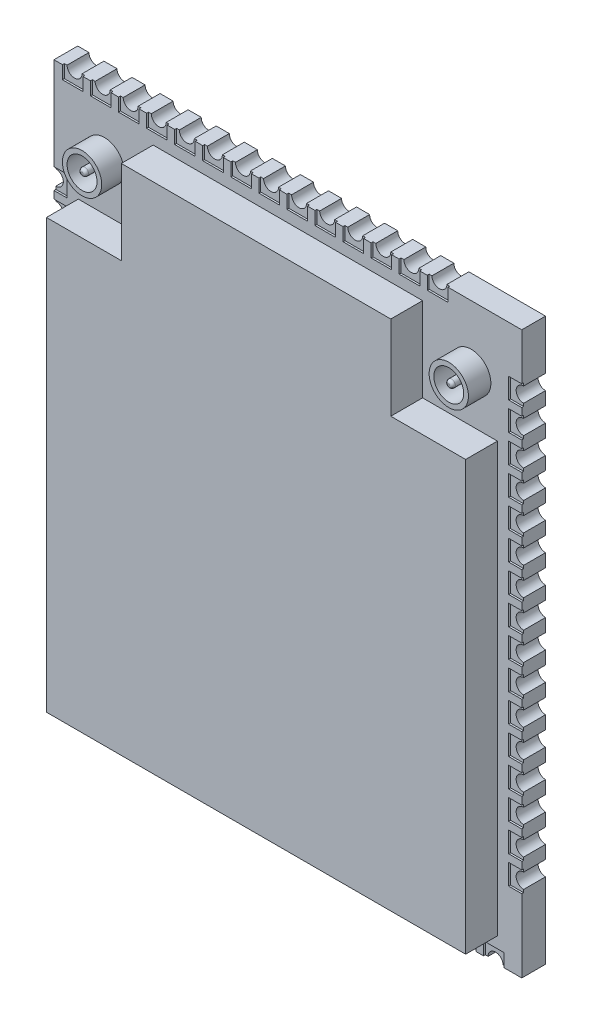
SolidWorks part; units mm, degrees
ref_plane "Front Plane" through (0, 0, 0) normal (0, 0, 1) x (1, 0, 0)
ref_plane "Top Plane" through (0, 0, 0) normal (0, 1, 0) x (1, 0, 0)
ref_plane "Right Plane" through (0, 0, 0) normal (1, 0, 0) x (0, 0, -1)
sketch "Sketch1" plane through (0, 0, 0) normal (0, 0, 1) x (1, 0, 0)
  line L1 (0, 0) -> (25, 0)
  line L2 (0, 0) -> (0, 30)
  line L3 (0, 30) -> (25, 30)
  line L4 (25, 0) -> (25, 30)
  dimension "D1" = 30
  dimension "D2" = 25
extrude "Boss-Extrude1" add sketch "Sketch1" along normal blind 1.27
sketch "Sketch2" plane through (0, 0, 1.27) normal (0, 0, 1) x (1, 0, 0)
  line L0 (0, 30) -> (0, 0) construction
  line L1 (5.3, 28.7) -> (19.7, 28.7)
  line L2 (1.3, 24.2) -> (1.3, 1.3)
  line L3 (1.3, 1.3) -> (23.7, 1.3)
  line L4 (23.7, 24.2) -> (23.7, 1.3)
  line L5 (25, 0) -> (25, 30) construction
  line L6 (25, 30) -> (0, 30) construction
  line L7 (0, 0) -> (25, 0) construction
  line L11 (23.7, 24.2) -> (19.7, 24.2)
  line L12 (19.7, 28.7) -> (19.7, 24.2)
  line L15 (1.3, 24.2) -> (5.3, 24.2)
  line L16 (5.3, 28.7) -> (5.3, 24.2)
  dimension "D1" = 1.3
  dimension "D2" = 1.3
  dimension "D3" = 1.3
  dimension "D4" = 1.3
  dimension "D5" = 4.5
  dimension "D6" = 4
  dimension "D7" = 4.5
  dimension "D8" = 4
extrude "Boss-Extrude2" add sketch "Sketch2" along normal blind 1.7
sketch "Sketch3" plane through (0, 0, 1.27) normal (0, 0, 1) x (1, 0, 0)
  line L0 (25, 30) -> (0, 30) construction
  line L1 (25, 0) -> (25, 30) construction
  circle A0 centre (22.3, 26.7) radius 0.8
  circle A1 centre (22.3, 26.7) radius 0.2
  circle A2 centre (22.3, 26.7) radius 1.05
  dimension "D3" = 0.4
  dimension "D4" = 2.1
  dimension "D5" = 1.6
  dimension "D1" = 3.3
  dimension "D2" = 2.7
extrude "Boss-Extrude3" add sketch "Sketch3" along normal blind 1.2 contours A2 A0 | A1
fillet "Fillet1" radius 0.15 1 edges at (22.5, 26.7, 2.47)
ref_plane "Plane1" through (12.5, 0, 0) normal (1, 0, 0) x (0, 0, -1)
mirror "Mirror1" about plane through (12.5, 0, 0) normal (1, 0, 0) of "Fillet1", "Boss-Extrude3"
ref_plane "Plane2" through (0, 5, 0) normal (0, 1, 0) x (1, 0, 0)
ref_plane "Plane3" through (0, 4.45, 0) normal (0, 1, 0) x (1, 0, 0)
ref_plane "Plane4" through (1, 0, 0) normal (1, 0, 0) x (0, 0, -1)
sketch "Sketch4" plane through (0, 0, 1.27) normal (0, 0, 1) x (1, 0, 0)
  line L0 (1.6335, 5) -> (-1.6335, 5) construction
  line L1 (0, 30) -> (0, 0) construction
  line L2 (0, 5.4) -> (0, 4.6)
  arc A0 (0, 5.4) -> (0, 4.6) centre (0, 5) cw
  dimension "D1" = 0.4
extrude "Cut-Extrude1" cut sketch "Sketch4" against normal up to next (1.27 mm away)
sketch "Sketch5" plane through (0, 0, 1.27) normal (0, 0, 1) x (1, 0, 0)
  line L0 (0, 5.55) -> (0.7, 5.55)
  line L1 (0, 30) -> (0, 5.4) construction
  line L2 (0.7, 5.55) -> (0.7, 4.45)
  line L3 (0.7, 4.45) -> (0, 4.45)
  line L4 (0, 4.6) -> (0, 0) construction
  line L5 (0, 4.45) -> (0, 5.55)
  line L6 (1.6335, 5) -> (-1.6335, 5) construction
  point P4 (0.7, 5)
  dimension "D1" = 1.1
  dimension "D2" = 0.7
extrude "Cut-Extrude2" cut sketch "Sketch5" against normal blind 0.1
pattern_linear "LPattern1" count 14 spacing 1.5 along (0, 1, 0) of "Cut-Extrude1", "Cut-Extrude2"
sketch "Sketch6" plane through (0, 0, 1.27) normal (0, 0, 1) x (1, 0, 0)
  line L0 (1, -1.6335) -> (1, 1.6335) construction
  line L1 (0, 0) -> (25, 0) construction
  line L2 (0.6, 0) -> (1.4, 0)
  arc A0 (0.6, 0) -> (1.4, 0) centre (1, 0) cw
  dimension "D1" = 0.4
extrude "Cut-Extrude3" cut sketch "Sketch6" against normal up to next (1.27 mm away)
sketch "Sketch7" plane through (0, 0, 1.27) normal (0, 0, 1) x (1, 0, 0)
  line L0 (1, -1.6335) -> (1, 1.6335) construction
  line L1 (0.45, 0) -> (1.55, 0)
  line L2 (0.45, 0) -> (0.45, 0.7)
  line L3 (0.45, 0.7) -> (1.55, 0.7)
  line L4 (1.55, 0) -> (1.55, 0.7)
  line L5 (1.4, 0) -> (25, 0) construction
  point P4 (1, 0.7)
  dimension "D1" = 0.7
  dimension "D2" = 1.1
extrude "Cut-Extrude4" cut sketch "Sketch7" against normal blind 0.1
sketch "Sketch9" plane through (0, 0, 1.27) normal (0, 0, 1) x (1, 0, 0)
  line L0 (1.6335, 4.45) -> (-1.6335, 4.45) construction
  line L1 (25, 0) -> (25, 30) construction
  line L2 (25, 4.85) -> (25, 4.05)
  arc A0 (25, 4.05) -> (25, 4.85) centre (25, 4.45) cw
  dimension "D1" = 0.4
extrude "Cut-Extrude5" cut sketch "Sketch9" against normal up to next (1.27 mm away)
sketch "Sketch10" plane through (0, 0, 1.27) normal (0, 0, 1) x (1, 0, 0)
  line L0 (25, 0) -> (25, 4.05) construction
  line L1 (25, 3.9) -> (24.3, 3.9)
  line L2 (25, 3.9) -> (25, 5)
  line L3 (25, 5) -> (24.3, 5)
  line L4 (24.3, 3.9) -> (24.3, 5)
  line L5 (1.6335, 4.45) -> (-1.6335, 4.45) construction
  point P6 (24.3, 4.45)
  dimension "D1" = 0.7
  dimension "D2" = 1.1
extrude "Cut-Extrude6" cut sketch "Sketch10" against normal blind 0.1
sketch "Sketch11" plane through (0, 0, 1.27) normal (0, 0, 1) x (1, 0, 0)
  line L0 (1, -1.6335) -> (1, 1.6335) construction
  line L1 (25, 30) -> (0, 30) construction
  line L2 (0.6, 30) -> (1.4, 30)
  arc A0 (0.6, 30) -> (1.4, 30) centre (1, 30) ccw
  dimension "D1" = 0.4
extrude "Cut-Extrude7" cut sketch "Sketch11" against normal up to next (1.27 mm away)
sketch "Sketch12" plane through (0, 0, 1.27) normal (0, 0, 1) x (1, 0, 0)
  line L0 (0.6, 30) -> (0, 30) construction
  line L1 (0.45, 30) -> (1.55, 30)
  line L2 (0.45, 30) -> (0.45, 29.3)
  line L3 (0.45, 29.3) -> (1.55, 29.3)
  line L4 (1.55, 30) -> (1.55, 29.3)
  line L5 (1, -1.6335) -> (1, 1.6335) construction
  point P6 (1, 29.3)
  dimension "D1" = 1.1
  dimension "D2" = 0.7
extrude "Cut-Extrude8" cut sketch "Sketch12" against normal blind 0.1
pattern_linear "LPattern2" count 16 spacing 1.5 along (1, 0, 0) of "Cut-Extrude3", "Cut-Extrude4"
pattern_linear "LPattern3" count 16 spacing 1.5 along (0, 1, 0) of "Cut-Extrude5", "Cut-Extrude6"
pattern_linear "LPattern4" count 14 spacing 1.5 along (1, 0, 0) of "Cut-Extrude7", "Cut-Extrude8"
